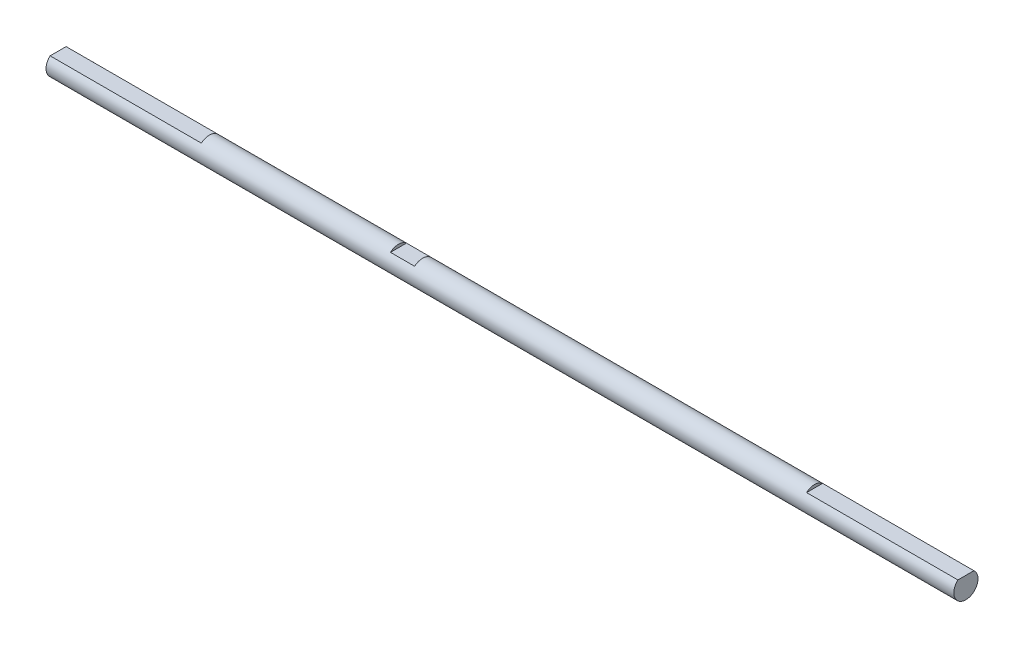
SolidWorks part; units mm, degrees
material "Plain Carbon Steel"
ref_plane "Front Plane" through (0, 0, 0) normal (0, 0, 1) x (1, 0, 0)
ref_plane "Top Plane" through (0, 0, 0) normal (0, 1, 0) x (1, 0, 0)
ref_plane "Right Plane" through (0, 0, 0) normal (1, 0, 0) x (0, 0, -1)
sketch "Sketch1" plane through (0, 0, 0) normal (1, 0, 0) x (0, 0, -1)
  line L0 (-1.3229, 1.5) -> (1.3229, 1.5)
  arc A0 (-1.3229, 1.5) -> (1.3229, 1.5) centre (0, 0) ccw
  dimension "D1" = 4
  dimension "D2" = 1.5
extrude "Boss-Extrude1" add sketch "Sketch1" along normal mid plane 150
sketch "Sketch2" plane through (0, 0, 0) normal (1, 0, 0) x (0, 0, -1)
  circle A0 centre (0, 0) radius 2
  arc A1 (-1.3229, 1.5) -> (1.3229, 1.5) centre (0, 0) ccw construction
extrude "Boss-Extrude2" add sketch "Sketch2" along normal mid plane 100
sketch "Sketch3" plane through (0, 0, 0) normal (0, 0, 1) x (1, 0, 0)
  line L0 (50, 2) -> (-50, 2) construction
  line L1 (-18.76, 2) -> (-14.76, 2)
  line L2 (-18.76, 2) -> (-18.76, 1.5)
  line L3 (-18.76, 1.5) -> (-14.76, 1.5)
  line L4 (-14.76, 2) -> (-14.76, 1.5)
  line L5 (-50, 1.5) -> (-75, 1.5) construction
  dimension "D1" = 4
  dimension "D2" = 14.76
extrude "Cut-Extrude1" cut sketch "Sketch3" against normal through all both and the other way through all
